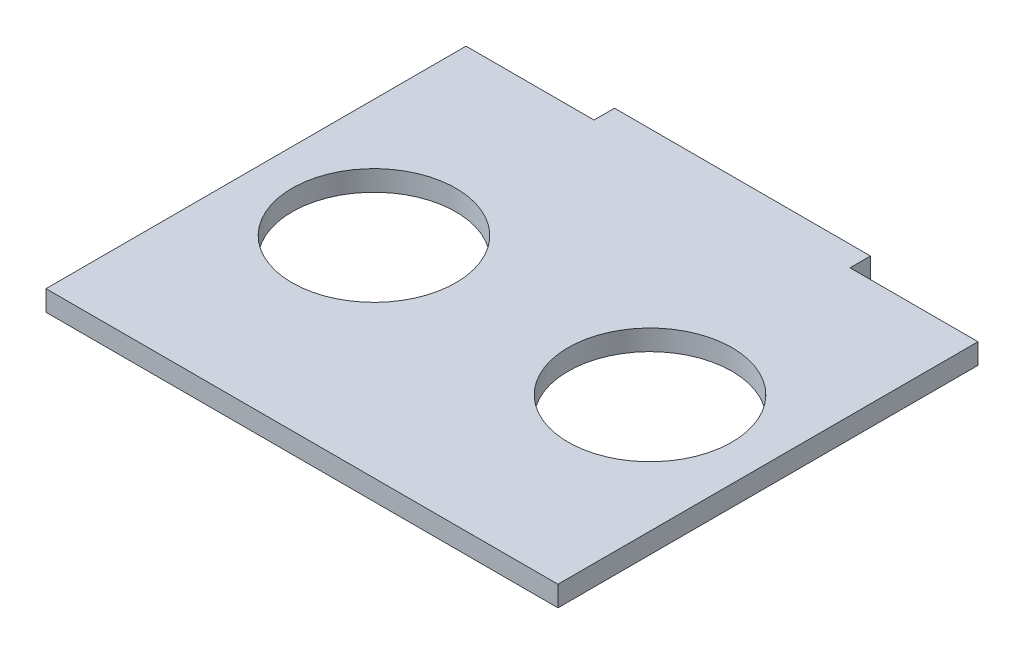
SolidWorks part; units mm, degrees
ref_plane "前基準面" through (0, 0, 0) normal (0, 0, 1) x (1, 0, 0)
ref_plane "上基準面" through (0, 0, 0) normal (0, 1, 0) x (1, 0, 0)
ref_plane "右基準面" through (0, 0, 0) normal (1, 0, 0) x (0, 0, -1)
sketch "草圖1" plane through (0, 0, 0) normal (0, 1, 0) x (1, 0, 0)
  line L0 (12.5, 20.5115) -> (25, 20.5115)
  line L1 (-22.25, -10.35) -> (22.25, -10.35) construction
  line L2 (-22.25, -10.35) -> (-22.25, 10.35) construction
  line L3 (-22.25, 10.35) -> (22.25, 10.35) construction
  line L4 (22.25, -10.35) -> (22.25, 10.35) construction
  line L5 (0, 10.35) -> (0, -10.35) construction
  line L6 (-22.25, 0) -> (22.25, 0) construction
  line L7 (-25, -20.5115) -> (25, -20.5115)
  line L8 (-25, -20.5115) -> (-25, 20.5115)
  line L9 (-25, 20.5115) -> (-12.5, 20.5115)
  line L10 (25, -20.5115) -> (25, 20.5115)
  line L11 (0, 20.5115) -> (0, -20.5115) construction
  line L12 (-25, 0) -> (25, 0) construction
  line L13 (-12.5, 22.5115) -> (12.5, 22.5115)
  line L14 (-12.5, 22.5115) -> (-12.5, 20.5115)
  line L16 (12.5, 22.5115) -> (12.5, 20.5115)
  line L17 (0, 20.5115) -> (0, 22.5115) construction
  line L18 (-12.5, 21.5115) -> (12.5, 21.5115) construction
  circle A0 centre (-13.48, 0) radius 8
  circle A1 centre (13.48, 0) radius 8
  point P0 (0, 0)
  point P8 (0, 0)
  point P12 (0, 21.5115)
  dimension "D2" = 16
  dimension "D1" = 26.96
  dimension "D3" = 44.5
  dimension "D4" = 20.7
  dimension "D5" = 2
  dimension "D6" = 25
  dimension "D7" = 41.0229
  dimension "D8" = 50
extrude "填料-伸長1" add sketch "草圖1" along normal blind 2
